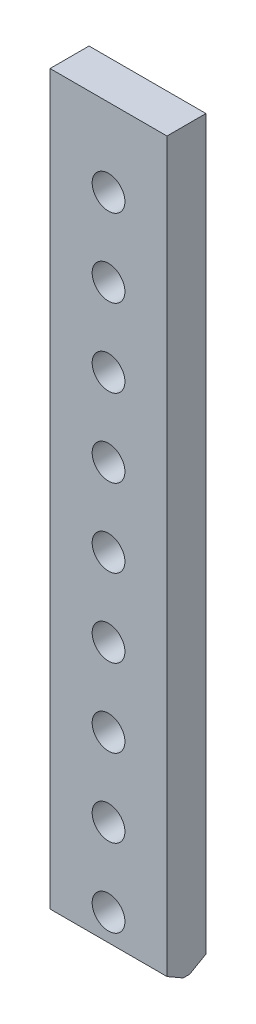
SolidWorks part; units mm, degrees
material "Простая углеродистая сталь"
ref_plane "Спереди" through (0, 0, 0) normal (0, 0, 1) x (1, 0, 0)
ref_plane "Сверху" through (0, 0, 0) normal (0, 1, 0) x (1, 0, 0)
ref_plane "Справа" through (0, 0, 0) normal (1, 0, 0) x (0, 0, -1)
sketch "Эскиз1" plane through (0, 0, 0) normal (0, 0, 1) x (1, 0, 0)
  line L1 (0, 0) -> (75, 0)
  line L2 (0, 0) -> (0, 473)
  line L3 (0, 473) -> (75, 473)
  line L4 (75, 0) -> (75, 473)
  point P5 (37.5, 473)
  dimension "D1" = 473
  dimension "D2" = 75
extrude "Бобышка-Вытянуть1" add sketch "Эскиз1" along normal blind 25
sketch "Эскиз2" plane through (0, 0, 25) normal (0, 0, 1) x (1, 0, 0)
  line L0 (0, 0) -> (75, 0) construction
  line L1 (75, 0) -> (75, 473) construction
  circle A0 centre (37.5, 23) radius 10.5
  circle A1 centre (37.5, 73) radius 10.5
  circle A2 centre (37.5, 123) radius 10.5
  circle A3 centre (37.5, 173) radius 10.5
  circle A4 centre (37.5, 223) radius 10.5
  circle A5 centre (37.5, 273) radius 10.5
  circle A6 centre (37.5, 323) radius 10.5
  circle A7 centre (37.5, 373) radius 10.5
  circle A8 centre (37.5, 423) radius 10.5
  dimension "D1" = 9
  dimension "D2" = 23
  dimension "D3" = 37.5
  dimension "D4" = 21
extrude "Вырез-Вытянуть1" cut sketch "Эскиз2" against normal through all
chamfer "Фаска1" distance 6 angle 60 1 edges at (37.5, 0, 0)
chamfer "Фаска2" distance 6 angle 60 1 edges at (37.5, 0, 25)
